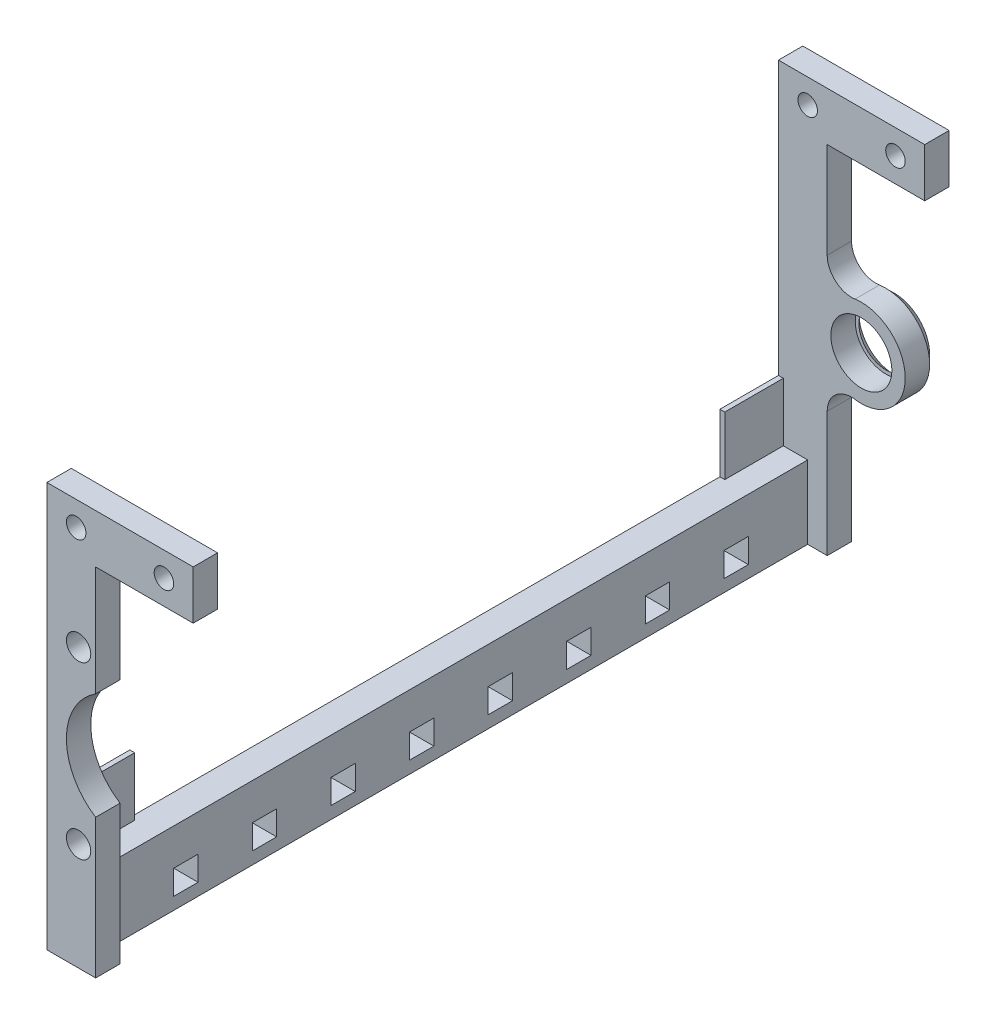
SolidWorks part; units mm, degrees
ref_plane "Plano frontal" through (0, 0, 0) normal (0, 0, 1) x (1, 0, 0)
ref_plane "Plano superior" through (0, 0, 0) normal (0, 1, 0) x (1, 0, 0)
ref_plane "Plano direito" through (0, 0, 0) normal (1, 0, 0) x (0, 0, -1)
sketch "Esboço1" plane through (0, 0, 0) normal (0, 0, 1) x (1, 0, 0)
  line L0 (7, 39.5) -> (-10, 39.5) construction
  line L1 (0, 0) -> (-10, 0)
  line L2 (0, 0) -> (0, 28.5455)
  line L3 (0, 83) -> (-10, 83)
  line L4 (-10, 0) -> (-10, 83)
  line L5 (0, 83) -> (20, 83)
  line L6 (0, 50.4545) -> (0, 73)
  line L7 (20, 83) -> (20, 73)
  line L8 (20, 73) -> (0, 73)
  line L9 (-3.5, 57) -> (14.5, 57) construction
  circle A0 centre (-3.5, 57) radius 2.5
  circle A1 centre (-3.5, 22) radius 2.5
  arc A2 (0, 28.5455) -> (0, 50.4545) centre (7, 39.5) cw
  circle A3 centre (14.5, 57) radius 2.5
  circle A4 centre (14, 78) radius 2
  circle A5 centre (-4, 78) radius 2
  point P22 (0, 0)
  point P23 (0, 0)
  dimension "D3" = 5
  dimension "D4" = 35
  dimension "D5" = 13
  dimension "D12" = 83
  dimension "D13" = 4
  dimension "D2" = 10
  dimension "D6" = 17
  dimension "D7" = 26
  dimension "D8" = 3.5
  dimension "D9" = 20
  dimension "D10" = 10
  dimension "D11" = 18
  dimension "D14" = 18
  dimension "D15" = 6
extrude "Ressalto-extrusão1" add sketch "Esboço1" along normal blind 5
sketch "Esboço3" plane through (-10, 0, 0) normal (-1, 0, 0) x (0, 0, 1)
  line L0 (-31.1175, 2.5) -> (-36.1175, 2.5)
  line L1 (0, 0) -> (-145, 0)
  line L2 (0, 0) -> (0, 15)
  line L3 (0, 15) -> (-145, 15)
  line L4 (-145, 0) -> (-145, 15)
  line L5 (-31.1175, 2.5) -> (-31.1175, 7.5)
  line L6 (-15, 2.5) -> (-20, 2.5)
  line L7 (-15, 2.5) -> (-15, 7.5)
  line L8 (-15, 7.5) -> (-20, 7.5)
  line L9 (-20, 2.5) -> (-20, 7.5)
  line L10 (-31.1175, 7.5) -> (-36.1175, 7.5)
  line L11 (-36.1175, 2.5) -> (-36.1175, 7.5)
  line L12 (-47.2351, 2.5) -> (-52.2351, 2.5)
  line L13 (-47.2351, 2.5) -> (-47.2351, 7.5)
  line L14 (-47.2351, 7.5) -> (-52.2351, 7.5)
  line L15 (-52.2351, 2.5) -> (-52.2351, 7.5)
  line L16 (-63.3526, 2.5) -> (-68.3526, 2.5)
  line L17 (-63.3526, 2.5) -> (-63.3526, 7.5)
  line L18 (-63.3526, 7.5) -> (-68.3526, 7.5)
  line L19 (-68.3526, 2.5) -> (-68.3526, 7.5)
  line L20 (-79.4702, 2.5) -> (-84.4702, 2.5)
  line L21 (-79.4702, 2.5) -> (-79.4702, 7.5)
  line L22 (-79.4702, 7.5) -> (-84.4702, 7.5)
  line L23 (-84.4702, 2.5) -> (-84.4702, 7.5)
  line L24 (-95.5877, 2.5) -> (-100.5877, 2.5)
  line L25 (-95.5877, 2.5) -> (-95.5877, 7.5)
  line L26 (-95.5877, 7.5) -> (-100.5877, 7.5)
  line L27 (-100.5877, 2.5) -> (-100.5877, 7.5)
  line L28 (-111.7052, 2.5) -> (-116.7052, 2.5)
  line L29 (-111.7052, 2.5) -> (-111.7052, 7.5)
  line L30 (-111.7052, 7.5) -> (-116.7052, 7.5)
  line L31 (-116.7052, 2.5) -> (-116.7052, 7.5)
  line L32 (-127.8228, 2.5) -> (-132.8228, 2.5)
  line L33 (-127.8228, 2.5) -> (-127.8228, 7.5)
  line L34 (-127.8228, 7.5) -> (-132.8228, 7.5)
  line L35 (-132.8228, 2.5) -> (-132.8228, 7.5)
  point P5 (0, 0)
  point P6 (0, 0)
  point P11 (0, 0)
  point P42 (0, 0)
  point P44 (0, 0)
  point P45 (0, 0)
  point P46 (0, 0)
  point P48 (0, 0)
  point P49 (0, 0)
  point P51 (0, 0)
  dimension "D1" = 145
  dimension "D2" = 15
  dimension "D3" = 5
  dimension "D4" = 5
  dimension "D5" = 15
  dimension "D7" = 2.5
  dimension "D6" = 8
extrude "Ressalto-extrusão3" add sketch "Esboço3" against normal blind 6
sketch "Esboço4" plane through (0, 0, -145) normal (0, 0, -1) x (-1, 0, 0)
  line L0 (6, 39.5) -> (1.9721, 39.5) construction
  line L1 (10, 0) -> (0, 0)
  line L2 (10, 0) -> (10, 30.9645)
  line L3 (10, 83) -> (0, 83)
  line L4 (0, 0) -> (0, 25.6436)
  line L5 (0, 83) -> (-20, 83)
  line L6 (-20, 83) -> (-20, 73)
  line L7 (10, 83) -> (10, 30.9645)
  line L8 (-20, 73) -> (0, 73)
  line L9 (0, 73) -> (0, 53.3564)
  circle A0 centre (-7, 39.5) radius 6.25
  circle A1 centre (-14, 78) radius 2 construction
  arc A2 (0, 28.5455) -> (0, 50.4545) centre (-7, 39.5) ccw construction
  arc A3 (-5.7143, 48.4077) -> (-5.7143, 30.5923) centre (-7, 39.5) ccw
  arc A4 (-5.7143, 30.5923) -> (0, 25.6436) centre (-5, 25.6436) cw
  circle A6 centre (-14, 78) radius 2
  arc A7 (-5.7143, 48.4077) -> (0, 53.3564) centre (-5, 53.3564) ccw
  circle A8 centre (4, 78) radius 2
  dimension "D3" = 12.5
  dimension "D5" = 18
  dimension "D2" = 5
  dimension "D4" = 5
extrude "Ressalto-extrusão4" add sketch "Esboço4" along normal blind 5
sketch "Esboço5" plane through (0, 0, -150) normal (0, 0, -1) x (-1, 0, 0)
  circle A0 centre (-7, 39.5) radius 9
  circle A1 centre (-7, 39.5) radius 5.5
  arc A2 (-5.7143, 48.4077) -> (-5.7143, 30.5923) centre (-7, 39.5) ccw construction
extrude "Ressalto-extrusão5" add sketch "Esboço5" along normal blind 10 draft 45
sketch "Esboço6" plane through (-10, 0, 0) normal (-1, 0, 0) x (0, 0, 1)
  line L0 (-145, 27) -> (-133, 27)
  line L1 (-145, 15) -> (-145, 83) construction
  line L2 (-133, 27) -> (-133, 15)
  line L3 (0, 15) -> (-145, 15) construction
  line L4 (-133, 15) -> (-145, 15)
  line L5 (-145, 15) -> (-145, 27)
  line L7 (0, 27) -> (-12, 27)
  line L8 (0, 15) -> (0, 83) construction
  line L9 (-12, 27) -> (-12, 15)
  line M5 (0, 83) -> (0, 15)
  line M6 (0, 15) -> (-145, 15)
  line M7 (-145, 15) -> (-145, 83)
  dimension "D1" = 12
extrude "Ressalto-extrusão6" add sketch "Esboço6" against normal blind 1 separate body contours L2 L0 M7 M6 | L7 L9 M6 M5
